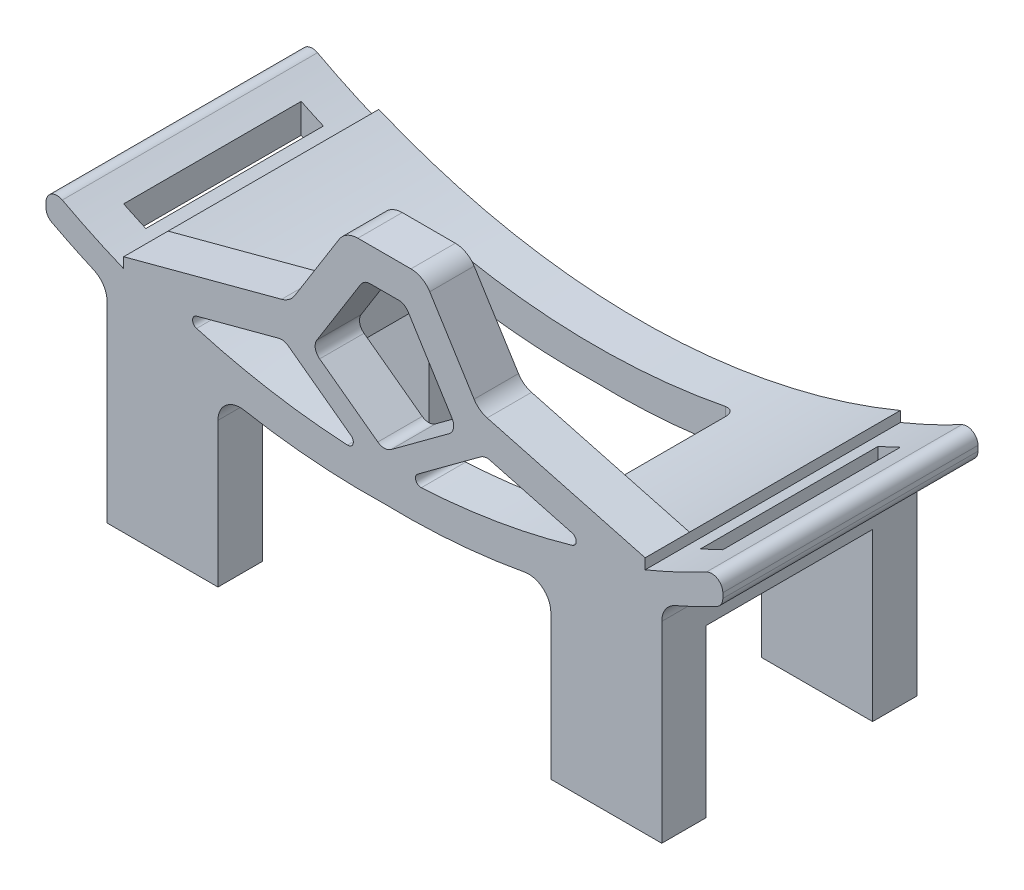
SolidWorks part; units mm, degrees
ref_plane "前视基准面" through (0, 0, 0) normal (0, 0, 1) x (1, 0, 0)
ref_plane "上视基准面" through (0, 0, 0) normal (0, 1, 0) x (1, 0, 0)
ref_plane "右视基准面" through (0, 0, 0) normal (1, 0, 0) x (0, 0, -1)
sketch "草图1" plane through (0, 0, 0) normal (0, 1, 0) x (1, 0, 0)
  line L1 (-59.9987, -12.8668) -> (1.0013, -12.8668)
  line L2 (-59.9987, -12.8668) -> (-59.9987, -35.8668)
  line L3 (-59.9987, -35.8668) -> (1.0013, -35.8668)
  line L4 (1.0013, -12.8668) -> (1.0013, -35.8668)
  line L5 (-59.9987, -16.8668) -> (1.0013, -16.8668)
  line L6 (-59.9987, -16.8668) -> (-59.9987, -31.8668)
  line L7 (-59.9987, -31.8668) -> (1.0013, -31.8668)
  line L8 (1.0013, -16.8668) -> (1.0013, -31.8668)
  dimension "D1" = 15
  dimension "D2" = 4
  dimension "D3" = 4
  dimension "D4" = 61
extrude "凸台-拉伸1" add sketch "草图1" along normal blind 15 contours L2 L5 L4 L1 | L7 L2 L3 L4
sketch "草图2" plane through (0, 15, 0) normal (0, 1, 0) x (1, 0, 0)
  line L1 (-59.9987, -12.8668) -> (1.0013, -12.8668)
  line L2 (-59.9987, -12.8668) -> (-59.9987, -35.8668)
  line L3 (-59.9987, -35.8668) -> (1.0013, -35.8668)
  line L4 (1.0013, -12.8668) -> (1.0013, -35.8668)
extrude "凸台-拉伸2" add sketch "草图2" along normal blind 4
sketch "草图3" plane through (0, 0, 35.8668) normal (0, 0, 1) x (1, 0, 0)
  line L1 (-59.9987, 19) -> (1.0013, 19)
  line L2 (-59.9987, 19) -> (-59.9987, 25)
  line L3 (-59.9987, 25) -> (1.0013, 25)
  line L4 (1.0013, 19) -> (1.0013, 25)
  arc A0 (-59.9987, 25) -> (1.0013, 25) centre (-29.4987, 77.8275) ccw
  line M5 (1.0013, 19) -> (-59.9987, 19)
  dimension "D1" = 61
  dimension "D2" = 6
extrude "凸台-拉伸3" add sketch "草图3" against normal blind 23 contours A0 L2 M5 | A0 L4 M5
sketch "草图4" plane through (0, 0, 35.8668) normal (0, 0, 1) x (1, 0, 0)
  line L0 (-59.9987, 25) -> (1.0013, 25)
  arc A0 (-59.9987, 25) -> (1.0013, 25) centre (-29.4987, 77.8275) ccw
extrude "切除-拉伸1" cut sketch "草图4" against normal blind 23
ref_plane "基准面1" through (-29.4987, 0, 0) normal (-1, 0, 0) x (0, 0, 1)
sketch "草图7" plane through (0, 0, 35.8668) normal (0, 0, 1) x (1, 0, 0)
  line L0 (-44.4987, 0) -> (-29.4987, 0)
  line L1 (-59.9987, 0) -> (1.0013, 0) construction
  line L2 (-29.4987, 0) -> (-29.4987, 14)
  line L3 (-54.4987, 0) -> (-54.4987, 17.3226)
  line L4 (-44.4987, 0) -> (-44.4987, 13.0174)
  line L5 (-59.9987, 25) -> (-59.9987, 0) construction
  line L6 (-59.9987, 21.2551) -> (-59.9987, 0)
  line L7 (-59.9987, 0) -> (-54.4987, 0)
  arc A0 (-42.1371, 14.9844) -> (-29.4987, 14) centre (-31.1065, 74.9788) ccw
  arc A1 (-44.4987, 13.0174) -> (-42.1371, 14.9844) centre (-42.4987, 13.0174) cw
  arc A2 (-55.6926, 19.153) -> (-59.9987, 21.2551) centre (-31.1065, 74.9788) cw
  arc A3 (-54.4987, 17.3226) -> (-55.6926, 19.153) centre (-56.4987, 17.3226) ccw
  dimension "D1" = 61
  dimension "D4" = 2
  dimension "D5" = 10
  dimension "D6" = 2
  dimension "D2" = 14
  dimension "D3" = 15
extrude "切除-拉伸2" cut sketch "草图7" against normal blind 23
sketch "草图8" plane through (0, 0, 35.8668) normal (0, 0, 1) x (1, 0, 0)
  line L0 (-59.9987, 25) -> (-59.9987, 21.2551) construction
  line L1 (-59.9987, 24) -> (-59.9987, 25)
  line L2 (-59.9987, 25) -> (-52.9987, 25)
  line L3 (-52.9987, 25) -> (-52.9987, 20.5964)
  arc A0 (-59.9987, 24) -> (-52.9987, 20.5964) centre (-29.4987, 77.8275) ccw
  arc A1 (-59.9987, 25) -> (1.0013, 25) centre (-29.4987, 77.8275) ccw construction
  dimension "D1" = 1
  dimension "D2" = 7
extrude "切除-拉伸3" cut sketch "草图8" against normal blind 23
fillet "圆角1" radius 1 2 edges at (-59.9987, 21.2551, 24.3668) (-59.9987, 24, 24.3668)
sketch "草图9" plane through (0, 0, 0) normal (0, -1, 0) x (1, 0, 0)
  line L0 (-54.4987, 35.8668) -> (-54.4987, 31.8668) construction
  line L1 (-54.4987, 32.3668) -> (-56.4987, 32.3668)
  line L2 (-54.4987, 32.3668) -> (-54.4987, 16.3668)
  line L3 (-54.4987, 16.3668) -> (-56.4987, 16.3668)
  line L4 (-56.4987, 32.3668) -> (-56.4987, 16.3668)
  line L6 (-54.4987, 35.8668) -> (-55.6926, 35.8668) construction
  dimension "D1" = 16
  dimension "D2" = 3.5
  dimension "D3" = 2
extrude "切除-拉伸4" cut sketch "草图9" against normal blind 40
mirror "镜向3" about plane through (-29.4987, 0, 0) normal (-1, 0, 0) of "切除-拉伸2"
mirror "镜向4" about plane through (-29.4987, 0, 0) normal (-1, 0, 0) of "切除-拉伸3"
fillet "圆角2" radius 1 2 edges at (1.0013, 24, 24.3668) (1.0013, 21.2551, 24.3668)
mirror "镜向7" about plane through (-29.4987, 0, 0) normal (-1, 0, 0) of "切除-拉伸4"
sketch "草图10" plane through (0, 0, 0) normal (0, -1, 0) x (1, 0, 0)
  line L1 (-42.2355, 31.8668) -> (-16.762, 31.8668)
  line L2 (-42.2355, 31.8668) -> (-42.2355, 16.8668)
  line L3 (-42.2355, 16.8668) -> (-16.762, 16.8668)
  line L4 (-16.762, 31.8668) -> (-16.762, 16.8668)
extrude "切除-拉伸5" cut sketch "草图10" against normal blind 40
fillet "圆角3" radius 1 4 edges at (-16.762, 16.586, 16.8668) (-42.2355, 16.586, 16.8668) (-42.2355, 16.586, 31.8668) (-16.762, 16.586, 31.8668)
sketch "草图11" plane through (0, 0, 35.8668) normal (0, 0, 1) x (1, 0, 0)
  line L0 (-52.9987, 21.5359) -> (-38.7612, 25.3326)
  line L1 (-37.5805, 26.205) -> (-33.5862, 32.5959)
  line L2 (-31.8902, 33.5359) -> (-27.1072, 33.5359)
  line L3 (-25.4112, 32.5959) -> (-21.4169, 26.205)
  line L4 (-20.2363, 25.3326) -> (-5.9987, 21.5359)
  arc A0 (-52.9987, 21.5359) -> (-5.9987, 21.5359) centre (-29.4987, 77.8275) ccw
  arc A1 (-38.7612, 25.3326) -> (-37.5805, 26.205) centre (-39.2765, 27.265) ccw
  arc A2 (-21.4169, 26.205) -> (-20.2363, 25.3326) centre (-19.7209, 27.265) ccw
  arc A3 (-27.1072, 33.5359) -> (-25.4112, 32.5959) centre (-27.1072, 31.5359) cw
  arc A4 (-33.5862, 32.5959) -> (-31.8902, 33.5359) centre (-31.8902, 31.5359) cw
  point P10 (-37.9987, 25.5359)
  point P16 (-20.9987, 25.5359)
  point P19 (-25.9987, 33.5359)
  point P22 (-32.9987, 33.5359)
  dimension "D8" = 2
  dimension "D1" = 15
  dimension "D2" = 15
  dimension "D3" = 5
  dimension "D4" = 5
  dimension "D5" = 12
  dimension "D6" = 4
  dimension "D7" = 4
extrude "凸台-拉伸4" add sketch "草图11" against normal blind 4
sketch "草图13" plane through (0, 0, 35.8668) normal (0, 0, 1) x (1, 0, 0)
  line L0 (-31.6297, 30.0659) -> (-35.591, 23.7278)
  line L1 (-39.022, 22.1582) -> (-46.4156, 20.1866)
  line L2 (-30.7817, 30.5359) -> (-28.2157, 30.5359)
  line L3 (-27.3677, 30.0659) -> (-23.4064, 23.7278)
  line L4 (-19.9754, 22.1582) -> (-12.5818, 20.1866)
  line L6 (-38.7612, 25.3326) -> (-52.9987, 21.5359) construction
  line L7 (-33.5862, 32.5959) -> (-37.5805, 26.205) construction
  line L8 (-21.4169, 26.205) -> (-25.4112, 32.5959) construction
  line L9 (-5.9987, 21.5359) -> (-20.2363, 25.3326) construction
  line L10 (-27.1072, 33.5359) -> (-31.8902, 33.5359) construction
  line L12 (-38.1713, 21.9971) -> (-32.5007, 17.8201)
  line L13 (-35.3361, 22.3927) -> (-30.0918, 18.5297)
  line L14 (-23.6614, 22.3927) -> (-28.9057, 18.5297)
  line L15 (-20.8262, 21.9971) -> (-26.4968, 17.8201)
  arc A0 (-46.4255, 19.2231) -> (-32.8245, 16.9183) centre (-29.4987, 77.8275) ccw
  arc A1 (-17.762, 17.9673) -> (-5.9987, 21.5359) centre (-29.4987, 77.8275) ccw construction
  arc A2 (-26.173, 16.9183) -> (-12.5719, 19.2231) centre (-29.4987, 77.8275) ccw
  arc A3 (-38.1713, 21.9971) -> (-39.022, 22.1582) centre (-38.7644, 21.1919) ccw
  arc A4 (-20.8262, 21.9971) -> (-19.9754, 22.1582) centre (-20.2331, 21.1919) cw
  arc A5 (-23.4064, 23.7278) -> (-23.6614, 22.3927) centre (-24.2544, 23.1978) cw
  arc A6 (-28.9057, 18.5297) -> (-30.0918, 18.5297) centre (-29.4987, 19.3349) cw
  arc A7 (-35.591, 23.7278) -> (-35.3361, 22.3927) centre (-34.743, 23.1978) ccw
  arc A8 (-28.2157, 30.5359) -> (-27.3677, 30.0659) centre (-28.2157, 29.5359) cw
  arc A9 (-31.6297, 30.0659) -> (-30.7817, 30.5359) centre (-30.7817, 29.5359) cw
  arc A10 (-12.5818, 20.1866) -> (-12.5719, 19.2231) centre (-12.7107, 19.7034) cw
  arc A11 (-26.173, 16.9183) -> (-26.4968, 17.8201) centre (-26.2002, 17.4175) cw
  arc A12 (-46.4156, 20.1866) -> (-46.4255, 19.2231) centre (-46.2868, 19.7034) ccw
  arc A13 (-32.5007, 17.8201) -> (-32.8245, 16.9183) centre (-32.7972, 17.4175) cw
  point P39 (0, 0)
  point P40 (0, 0)
  point P45 (-27.8126, 16.8509)
  dimension "D1" = 61
  dimension "D9" = 1
  dimension "D10" = 0.5
  dimension "D2" = 3
  dimension "D3" = 3
  dimension "D4" = 3
  dimension "D5" = 3
  dimension "D6" = 3
  dimension "D7" = 2
  dimension "D8" = 2
extrude "切除-拉伸6" cut sketch "草图13" against normal blind 40
